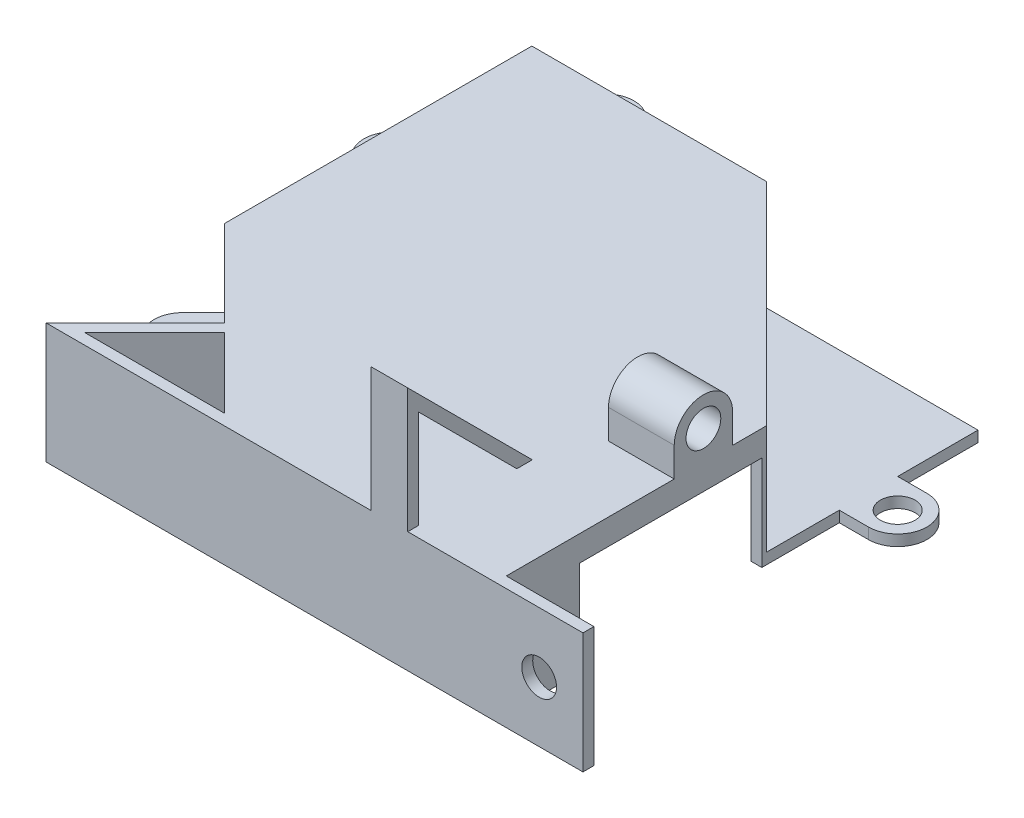
SolidWorks part; units mm, degrees
ref_plane "Front Plane" through (0, 0, 0) normal (0, 0, 1) x (1, 0, 0)
ref_plane "Top Plane" through (0, 0, 0) normal (0, 1, 0) x (1, 0, 0)
ref_plane "Right Plane" through (0, 0, 0) normal (1, 0, 0) x (0, 0, -1)
sketch "Sketch1" plane through (0, 0, 0) normal (0, 1, 0) x (1, 0, 0)
  line L0 (0, 0) -> (0, 40)
  line L1 (0, 40) -> (30, 40)
  line L2 (30, 40) -> (61.1127, 8.8873)
  line L3 (61.1127, 8.8873) -> (61.1127, -23.1127)
  line L4 (0, 0) -> (23.1127, -23.1127)
  line L5 (23.1127, -23.1127) -> (61.1127, -23.1127)
  line L6 (0, 40) -> (0, 41.5)
  line L7 (30, 40) -> (30, 41.5)
  line L8 (30, 40) -> (31.0607, 41.0607)
  line L9 (61.1127, 8.8873) -> (62.1734, 9.948)
  line L10 (61.1127, 8.8873) -> (62.6127, 8.8873)
  line L11 (61.1127, -23.1127) -> (62.6127, -23.1127)
  line L12 (61.1127, -23.1127) -> (61.1127, -24.6127)
  line L13 (23.1127, -23.1127) -> (23.1127, -24.6127)
  line L14 (0, 0) -> (-1.0607, -1.0607)
  line L15 (23.1127, -23.1127) -> (22.052, -24.1734)
  line L16 (0, 0) -> (-1.5, 0)
  line L17 (0, 40) -> (-1.5, 40)
  line L18 (23.1127, -24.6127) -> (62.6127, -24.6127)
  line L19 (62.6127, -24.6127) -> (62.6127, 10.1765)
  line L20 (31.0607, 41.0607) -> (62.6127, 9.5086)
  line L21 (31.0607, 41.0607) -> (29.4178, 42.7035)
  line L22 (0, 41.5) -> (30.6213, 41.5)
  line L23 (0, 41.5) -> (-1.5, 41.5)
  line L24 (-1.5, 41.5) -> (-1.5, -1.7336)
  line L25 (22.052, -24.1734) -> (-1.5, -0.6213)
  line L26 (22.052, -24.1734) -> (23.3539, -25.4752)
  line L27 (23.1127, -24.6127) -> (22.4914, -24.6127)
  line L28 (10.276, -12.3973) -> (-1.9393, -24.6127)
  line L29 (-1.9393, -24.6127) -> (22.4914, -24.6127)
  line L30 (10.276, -12.3973) -> (11.4081, -13.5294)
  line L31 (11.4081, -13.5294) -> (1.8248, -23.1127)
  line L32 (1.8248, -23.1127) -> (20.9914, -23.1127)
  dimension "D1" = 40
  dimension "D2" = 30
  dimension "D3" = 44
  dimension "D4" = 32
  dimension "D5" = 135
  dimension "D6" = 1.5
  dimension "D7" = 1.5
  dimension "D8" = 1.5
  dimension "D9" = 1.5
  dimension "D10" = 1.5
  dimension "D11" = 1.5
  dimension "D12" = 1.5
  dimension "D13" = 1.5
  dimension "D14" = 1.5
  dimension "D15" = 1.5
  dimension "D16" = 1.5
  dimension "D17" = 1.5
extrude "Boss-Extrude1" add sketch "Sketch1" along normal blind 15 contours L25 L15 L4 L14 | L27 L13 L15 L26 | L13 L18 L12 L5 | L18 L19 L11 L12 | L11 L19 L10 L3 | L20 L9 L10 L19 | L20 L8 L2 L9 | L22 L7 L8 L21 | L22 L6 L1 L7 | L23 L24 L17 L6 | L17 L24 L16 L0 | L25 L14 L16 L24 | L32 L31 L25 L28 L29 L26
sketch "Sketch2" plane through (0, 15, 0) normal (0, 1, 0) x (1, 0, 0)
  line L0 (-1.5, 41.5) -> (30.6213, 41.5)
  line L1 (30.6213, 41.5) -> (62.6127, 9.5086)
  line L2 (62.6127, 9.5086) -> (62.6127, -24.6127)
  line L3 (62.6127, -24.6127) -> (19.4814, -24.6127)
  line L4 (62.6127, -24.6127) -> (-1.9393, -24.6127) construction
  line L5 (-1.5, 41.5) -> (-1.5, -0.6213)
  line L6 (-1.5, -0.6213) -> (22.4914, -24.6127)
  line L7 (10.276, -12.3973) -> (-1.9393, -24.6127)
  line L8 (-1.9393, -24.6127) -> (22.4914, -24.6127)
  line L9 (11.4081, -13.5294) -> (1.8248, -23.1127)
  line L10 (1.8248, -23.1127) -> (20.9914, -23.1127)
  line M1 (62.6127, -24.6127) -> (62.6127, 9.5086)
  line M2 (62.6127, 9.5086) -> (30.6213, 41.5)
  line M3 (30.6213, 41.5) -> (-1.5, 41.5)
  line M4 (-1.5, 41.5) -> (-1.5, -0.6213)
  line M5 (-1.5, -0.6213) -> (10.276, -12.3973)
  line M6 (10.276, -12.3973) -> (-1.9393, -24.6127)
  line M7 (-1.9393, -24.6127) -> (62.6127, -24.6127)
  line M8 (30, 40) -> (61.1127, 8.8873)
  line M9 (61.1127, 8.8873) -> (61.1127, -23.1127)
  line M10 (61.1127, -23.1127) -> (23.1127, -23.1127)
  line M11 (23.1127, -23.1127) -> (0, 0)
  line M12 (0, 0) -> (0, 40)
  line M13 (0, 40) -> (30, 40)
  line M14 (11.4081, -13.5294) -> (20.9914, -23.1127)
  line M15 (20.9914, -23.1127) -> (1.8248, -23.1127)
  line M16 (1.8248, -23.1127) -> (11.4081, -13.5294)
extrude "Boss-Extrude2" add sketch "Sketch2" along normal blind 1.5 contours L6 L3 M5 M14 M1 M2 M3 M4 M13 M8 M9 M10 M11 M12 | M8 M13 M12 M11 M10 M9 | L6 M6 M7 M15 M16
sketch "Sketch7" plane through (62.6127, 0, 0) normal (1, 0, 0) x (0, 0, -1)
  line L0 (9.5086, 0) -> (9.5086, 12)
  line L1 (9.5086, 16.5) -> (9.5086, 0) construction
  line L2 (9.5086, 12) -> (-12.4914, 12)
  line L3 (-12.4914, 12) -> (-12.4914, 0)
  line L4 (-24.6127, 0) -> (9.5086, 0) construction
  line L5 (-12.4914, 0) -> (9.5086, 0)
  dimension "D1" = 12
  dimension "D2" = 22
extrude "Boss-Extrude4" add sketch "Sketch7" along normal blind 10.5
sketch "Sketch8" plane through (0, 0, -9.5086) normal (0, 0, -1) x (-1, 0, 0)
  line L0 (-73.1127, 0) -> (-61.1127, 0)
  line L1 (-61.1127, 0) -> (-61.1127, 6)
  line L2 (-61.1127, 6) -> (-65.6227, 6)
  circle A0 centre (-65.6227, 6) radius 4.5
  dimension "D4" = 9
  dimension "D1" = 12
  dimension "D2" = 6
  dimension "D3" = 4.51
sketch "Sketch9" plane through (61.1127, 0, 0) normal (-1, 0, 0) x (0, 0, 1)
  line L0 (23.1127, 0) -> (7.6127, 0)
  line L1 (-8.8873, 0) -> (23.1127, 0) construction
  line L2 (7.6127, 0) -> (7.6127, 2)
  line L3 (7.6127, 2) -> (-4.8873, 2)
  line L4 (-4.8873, 2) -> (-4.8873, 10.5)
  line L5 (-4.8873, 10.5) -> (7.6127, 10.5)
  line L6 (7.6127, 10.5) -> (7.6127, 2)
  dimension "D1" = 15.5
  dimension "D2" = 2
  dimension "D3" = 12.5
  dimension "D4" = 8.5
extrude "Cut-Extrude10" cut sketch "Sketch9" against normal blind 4.5 contours L6 L5 L4 L3
sketch "Sketch11" plane through (0, 0, 0) normal (0, -1, 0) x (1, 0, 0)
  line L0 (62.6127, -9.5086) -> (30.6213, -41.5)
  line L1 (30.6213, -41.5) -> (62.6127, -41.5)
  line L2 (62.6127, -41.5) -> (62.6127, -9.5086)
extrude "Boss-Extrude6" add sketch "Sketch11" against normal blind 1.5
sketch "Sketch12" plane through (62.6127, 0, 0) normal (1, 0, 0) x (0, 0, -1)
  line L0 (-7.552, 16.5) -> (-24.6127, 33.5607)
  line L1 (-24.6127, 16.5) -> (9.5086, 16.5) construction
  line L2 (-24.6127, 33.5607) -> (-24.6127, 16.5)
extrude "Extrude-Thin1" add sketch "Sketch12" along normal blind 5 from offset 20 thin offset against normal yes
sketch "Sketch13" plane through (0, 0, -9.5086) normal (0, 0, -1) x (-1, 0, 0)
  line L0 (-62.6127, 12) -> (-62.6127, 13)
  line L1 (-62.6127, 16.5) -> (-62.6127, 12) construction
  line L2 (-62.6127, 13) -> (-61.6127, 13)
  line L3 (-61.6127, 13) -> (-61.6127, 14)
  line L4 (-61.6127, 14) -> (-60.6127, 14)
  line L5 (-60.6127, 14) -> (-60.6127, 11)
  line L6 (-60.6127, 11) -> (-61.6127, 11)
  line L7 (-61.6127, 11) -> (-61.6127, 12)
  line L8 (-61.6127, 12) -> (-62.6127, 12)
  line L9 (-62.6127, 13) -> (-62.6127, 12)
  line L10 (-73.1127, 12) -> (-73.1127, 0)
  line L11 (-73.1127, 0) -> (-62.6127, 0)
  line L12 (-62.6127, 0) -> (-62.6127, 12)
  dimension "D1" = 1
  dimension "D2" = 1
  dimension "D3" = 3
  dimension "D4" = 1
  dimension "D5" = 1
  dimension "D6" = 1
sketch "Sketch16" plane through (0, 0, -9.5086) normal (0, 0, -1) x (-1, 0, 0)
  line L0 (-62.6127, 12) -> (-62.6127, 0)
  line L1 (-62.6127, 0) -> (-73.1127, 0)
  line L2 (-73.1127, 0) -> (-73.1127, 12)
  line L3 (-73.1127, 12) -> (-62.6127, 12)
extrude "Cut-Extrude15" cut sketch "Sketch16" against normal through all
sketch "Sketch19" plane through (0, 0, 0) normal (0, -1, 0) x (1, 0, 0)
  line L0 (61.1127, 23.1127) -> (58.1127, 23.1127)
  line L1 (23.1127, 23.1127) -> (61.1127, 23.1127) construction
  line L2 (58.1127, 23.1127) -> (59.6127, 23.1127)
  line L3 (59.6127, 23.1127) -> (59.6127, -10.3873)
  line L4 (30, -40) -> (61.1127, -8.8873) construction
  line L5 (58.1127, 23.1127) -> (58.1127, -11.8873)
  line L6 (30, -40) -> (61.1127, -8.8873) construction
  line L7 (58.1127, -11.8873) -> (59.6127, -10.3873)
extrude "Boss-Extrude10" add sketch "Sketch19" against normal blind 16
sketch "Sketch20" plane through (0, 0, 0) normal (0, -1, 0) x (1, 0, 0)
  line L0 (59.6127, 23.1127) -> (59.6127, 24.6127)
  line L1 (62.6127, 24.6127) -> (-1.9393, 24.6127) construction
  line L2 (59.6127, 24.6127) -> (62.6127, 24.6127)
  line L3 (62.6127, 24.6127) -> (62.6127, -41.5)
  line L4 (62.6127, -41.5) -> (59.6127, -41.5)
  line L5 (62.6127, -41.5) -> (-1.5, -41.5) construction
  line L6 (59.6127, -41.5) -> (59.6127, 23.1127)
extrude "Cut-Extrude16" cut sketch "Sketch20" against normal through all
sketch "Sketch21" plane through (0, 0, 0) normal (0, -1, 0) x (1, 0, 0)
  line L0 (58.1127, 23.1127) -> (58.1127, 13.1127)
  line L1 (58.1127, 23.1127) -> (58.1127, -11.8873) construction
  line L2 (58.1127, 13.1127) -> (59.6127, 13.1127)
  line L3 (59.6127, 24.6127) -> (59.6127, -41.5) construction
  line L4 (58.1127, 13.1127) -> (58.1127, -11.8873)
  line L5 (58.1127, -11.8873) -> (59.6127, -11.8873)
  line L6 (59.6127, -11.8873) -> (59.6127, 13.1127)
  line M3 (59.6127, -41.5) -> (59.6127, 24.6127)
  line M17 (58.1127, 23.1127) -> (58.1127, -11.8873)
extrude "Cut-Extrude17" cut sketch "Sketch21" against normal blind 13 contours L5 L2 M17 M3
sketch "Sketch25" plane through (59.6127, 0, 0) normal (1, 0, 0) x (0, 0, -1)
  line L0 (-24.6127, 16.5) -> (-23.1127, 16.5)
  line L1 (12.5086, 16.5) -> (-24.6127, 16.5) construction
  line L2 (-23.1127, 16.5) -> (-23.1127, 0)
  line L3 (-24.6127, 0) -> (-13.1127, 0) construction
  line L4 (-23.1127, 0) -> (-24.6127, 0)
  line L5 (-24.6127, 0) -> (-24.6127, 16.5)
extrude "Boss-Extrude13" add sketch "Sketch25" along normal blind 12
sketch "Sketch26" plane through (59.6127, 0, 0) normal (1, 0, 0) x (0, 0, -1)
  line L0 (-23.1127, 16.5) -> (3.8873, 16.5)
  line L1 (12.5086, 16.5) -> (-23.1127, 16.5) construction
  line L2 (3.8873, 16.5) -> (3.8873, 20.5)
  line L3 (7.8873, 20.5) -> (7.8873, 16.5)
  line L4 (7.8873, 16.5) -> (-0.1127, 16.5)
  line L5 (-0.1127, 16.5) -> (-0.1127, 20.5)
  arc A0 (7.8873, 20.5) -> (-0.1127, 20.5) centre (3.8873, 20.5) ccw
extrude "Boss-Extrude14" add sketch "Sketch26" against normal blind 9
sketch "Sketch27" plane through (59.6127, 0, 0) normal (1, 0, 0) x (0, 0, -1)
  line L0 (7.8873, 16.5) -> (3.8873, 16.5)
  line L1 (3.8873, 16.5) -> (3.8873, 20.5)
  circle A0 centre (3.8873, 20.5) radius 2.3813
extrude "Cut-Extrude18" cut sketch "Sketch27" against normal blind 6.35
sketch "Sketch29" plane through (0, 0, 23.1127) normal (0, 0, -1) x (-1, 0, 0)
  line L0 (-59.6127, 16.5) -> (-65.6127, 16.5)
  line L1 (-71.6127, 16.5) -> (-59.6127, 16.5) construction
  line L2 (-71.6127, 8.25) -> (-65.6127, 8.25)
  line L3 (-71.6127, 0) -> (-71.6127, 16.5) construction
  circle A0 centre (-65.6127, 8.25) radius 2.3813
extrude "Cut-Extrude19" cut sketch "Sketch29" against normal through all
sketch "Sketch30" plane through (0, 0, 0) normal (0, -1, 0) x (1, 0, 0)
  line L0 (-1.5, -41.5) -> (4.5, -41.5)
  line L1 (59.6127, -41.5) -> (-1.5, -41.5) construction
  line L2 (4.5, -41.5) -> (4.5, -45.5)
  line L3 (8.5, -45.5) -> (8.5, -41.5)
  line L4 (8.5, -41.5) -> (0.5, -41.5)
  line L5 (0.5, -41.5) -> (0.5, -45.5)
  arc A0 (0.5, -45.5) -> (8.5, -45.5) centre (4.5, -45.5) ccw
extrude "Boss-Extrude15" add sketch "Sketch30" against normal blind 9
sketch "Sketch31" plane through (0, 0, 0) normal (0, -1, 0) x (1, 0, 0)
  line L0 (-1.5, -41.5) -> (-1.5, -26.5)
  line L1 (-1.5, -41.5) -> (-1.5, 0.6213) construction
  line L2 (-1.5, -26.5) -> (-5.5, -26.5)
  line L3 (-5.5, -30.5) -> (-1.5, -30.5)
  line L4 (-1.5, -30.5) -> (-1.5, -22.5)
  line L5 (-1.5, -22.5) -> (-5.5, -22.5)
  arc A0 (-5.5, -30.5) -> (-5.5, -22.5) centre (-5.5, -26.5) cw
extrude "Boss-Extrude16" add sketch "Sketch31" against normal blind 9
sketch "Sketch32" plane through (0, 0, 0) normal (0, -1, 0) x (1, 0, 0)
  line L0 (-1.5, 0.6213) -> (4.388, 6.5093)
  line L1 (10.276, 12.3973) -> (-1.5, 0.6213) construction
  line L2 (4.388, 6.5093) -> (1.5596, 9.3378)
  line L3 (4.388, 12.1662) -> (7.2164, 9.3378)
  line L4 (7.2164, 9.3378) -> (1.5596, 3.6809)
  line L5 (1.5596, 3.6809) -> (-1.2688, 6.5093)
  arc A0 (-1.2688, 6.5093) -> (4.388, 12.1662) centre (1.5596, 9.3378) cw
extrude "Boss-Extrude17" add sketch "Sketch32" against normal blind 9
sketch "Sketch33" plane through (0, 0, 0) normal (0, -1, 0) x (1, 0, 0)
  line L0 (59.6127, -41.5) -> (59.6127, -26.5)
  line L1 (59.6127, -11.8873) -> (59.6127, -41.5) construction
  line L2 (59.6127, -26.5) -> (63.6127, -26.5)
  line L3 (63.6127, -30.5) -> (59.6127, -30.5)
  line L4 (59.6127, -30.5) -> (59.6127, -22.5)
  line L5 (59.6127, -22.5) -> (63.6127, -22.5)
  arc A0 (63.6127, -30.5) -> (63.6127, -22.5) centre (63.6127, -26.5) ccw
extrude "Boss-Extrude18" add sketch "Sketch33" against normal blind 1.5
sketch "Sketch34" plane through (0, 0, 0) normal (0, -1, 0) x (1, 0, 0)
  circle A0 centre (63.6127, -26.5) radius 2.3813
extrude "Cut-Extrude20" cut sketch "Sketch34" against normal through all
sketch "Sketch35" plane through (0, 0, 0) normal (0, -1, 0) x (1, 0, 0)
  circle A0 centre (4.5, -45.5) radius 2.3813
  circle A1 centre (-5.5, -26.5) radius 2.3813
  circle A2 centre (1.5596, 9.3378) radius 2.3813
extrude "Cut-Extrude21" cut sketch "Sketch35" against normal blind 6.35 contours A0 | A1 | A2
